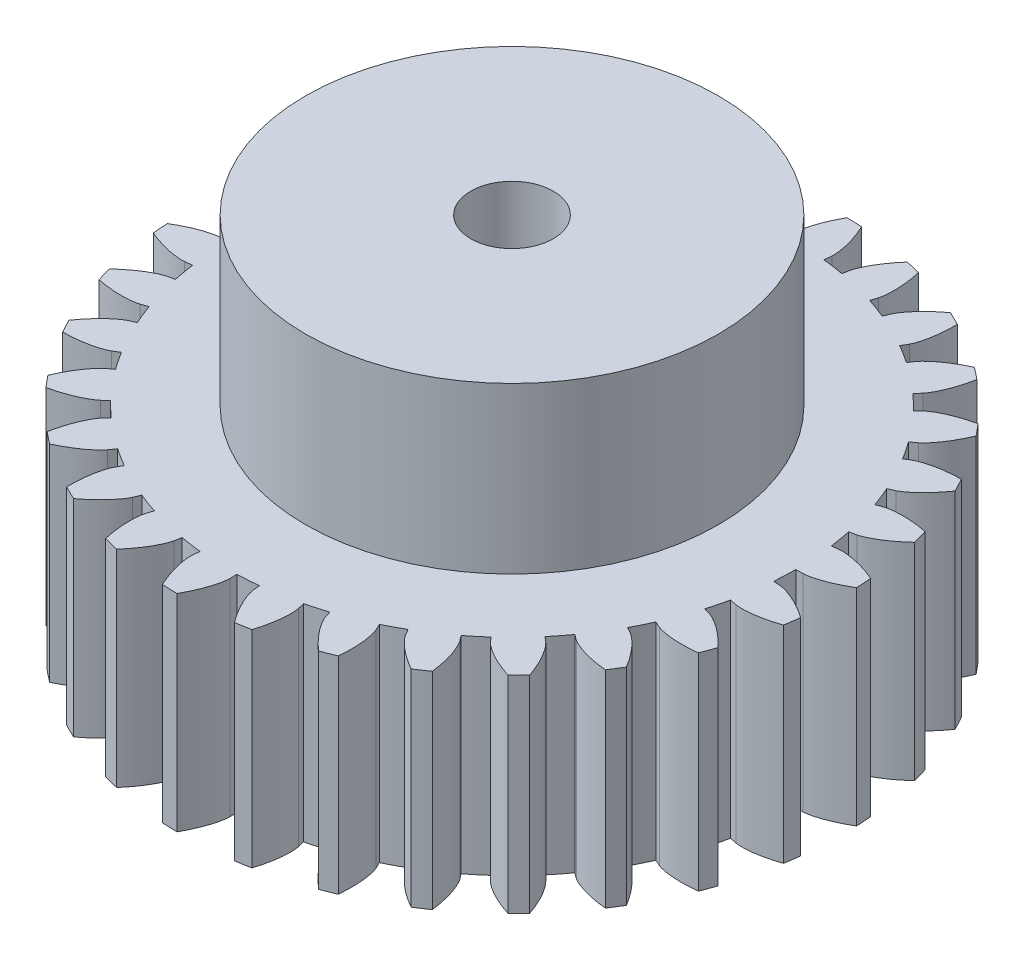
SolidWorks part; units mm, degrees
ref_plane "前视基准面" through (0, 0, 0) normal (0, 0, 1) x (1, 0, 0)
ref_plane "上视基准面" through (0, 0, 0) normal (0, 1, 0) x (1, 0, 0)
ref_plane "右视基准面" through (0, 0, 0) normal (1, 0, 0) x (0, 0, -1)
sketch "草图2" plane through (0, 0, 0) normal (0, 1, 0) x (1, 0, 0)
  line L0 (0, 0) -> (15.9638, 1.0755) construction
  line L1 (14.0954, 0) -> (13.75, 0)
  line L2 (13.968, 1.8907) -> (13.6257, 1.8444)
  circle A0 centre (0, 0) radius 14.0954
  circle A3 centre (0, 0) radius 13.75
  circle A4 centre (0, 0) radius 15
  circle A5 centre (0, 0) radius 16
  spline S0 degree 4 poles (14.0954, 0) (14.1222, 0.001) (14.1757, 0.0047) (14.282, 0.0185) (14.4824, 0.0575) (14.7468, 0.1297) (15.2365, 0.3049) (15.9787, 0.6703) (16.9045, 1.2915) (18.0602, 2.3363) (19.2165, 3.7493) (20.2505, 5.4679) (21.0984, 7.4555) (21.6937, 9.5315) (22.0508, 11.6608) (22.1898, 13.9217) (22.0692, 16.7242) (21.4978, 20.0254) (20.2807, 23.7245) (18.3101, 27.575) (15.8075, 31.1006) (13.2224, 33.8607) (10.7707, 35.9743) (8.5921, 37.5608) (6.7761, 38.7229) (4.4249, 40.0398) (1.9778, 41.1737) (-0.5458, 42.1227) (-3.6473, 43.04) (-6.016, 43.5621) (-8.1479, 43.8984) (-10.0201, 44.098) (-10.9657, 44.1742) (-11.7603, 44.2229) (-12.4935, 44.254) (-13.0612, 44.2726) (-13.8709, 44.2836) (-14.4735, 44.2825) (-15.466, 44.2663) (-16.2281, 44.2324) (-17.1613, 44.1817) (-17.9874, 44.1143) (-18.88, 44.0303) (-19.723, 43.9299) (-20.3853, 43.8424) (-20.8055, 43.7787) (-21.0244, 43.7455) knots 0 0 0 0 0 0.001401 0.002802 0.005604 0.010661 0.015718 0.02996 0.048734 0.068727 0.096889 0.125051 0.153212 0.181374 0.209535 0.237696 0.271429 0.327752 0.384075 0.440398 0.496721 0.553044 0.581206 0.609367 0.637529 0.66569 0.722013 0.750174 0.778336 0.834659 0.84874 0.86282 0.876901 0.883942 0.890982 0.900036 0.909091 0.920455 0.931818 0.943182 0.954545 0.965909 0.977273 0.988636 1 1 1 1 1 construction
  spline S1 degree 4 poles (14.0954, 0) (14.1222, 0.001) (14.1757, 0.0047) (14.282, 0.0185) (14.4824, 0.0575) (14.7468, 0.1297) (15.2365, 0.3049) (15.9787, 0.6703) (16.9045, 1.2915) (18.0602, 2.3363) (19.2165, 3.7493) (20.2505, 5.4679) (21.0984, 7.4555) (21.6937, 9.5315) (22.0508, 11.6608) (22.1898, 13.9217) (22.0692, 16.7242) (21.4978, 20.0254) (20.2807, 23.7245) (18.3101, 27.575) (15.8075, 31.1006) (13.2224, 33.8607) (10.7707, 35.9743) (8.5921, 37.5608) (6.7761, 38.7229) (4.4249, 40.0398) (1.9778, 41.1737) (-0.5458, 42.1227) (-3.6473, 43.04) (-6.016, 43.5621) (-8.1479, 43.8984) (-10.0201, 44.098) (-10.9657, 44.1742) (-11.7603, 44.2229) (-12.4935, 44.254) (-13.0612, 44.2726) (-13.6189, 44.2802) (-13.9379, 44.282) (-14.0954, 44.282) knots 0 0 0 0 0 0.001401 0.002802 0.005604 0.010661 0.015718 0.02996 0.048734 0.068727 0.096889 0.125051 0.153212 0.181374 0.209535 0.237696 0.271429 0.327752 0.384075 0.440398 0.496721 0.553044 0.581206 0.609367 0.637529 0.66569 0.722013 0.750174 0.778336 0.834659 0.84874 0.86282 0.876901 0.883942 0.890982 0.900036 0.909091 0.909091 0.909091 0.909091 0.909091
  spline S2 degree 4 poles (13.968, 1.8907) (13.9947, 1.8933) (14.0482, 1.8968) (14.1555, 1.8974) (14.3592, 1.8857) (14.631, 1.8495) (15.1397, 1.7416) (15.9242, 1.4791) (16.925, 0.9877) (18.2104, 0.1074) (19.5457, -1.1378) (20.801, -2.7021) (21.9077, -4.558) (22.7762, -6.5355) (23.4156, -8.5976) (23.8567, -10.8194) (24.1131, -13.6128) (23.9896, -16.9607) (23.2797, -20.7897) (21.8434, -24.8698) (19.8364, -28.6992) (17.6449, -31.7811) (15.4989, -34.2045) (13.5528, -36.0688) (11.909, -37.4641) (9.7557, -39.0844) (7.4828, -40.5363) (5.1093, -41.8153) (2.1589, -43.1402) (-0.1183, -43.9754) (-2.1859, -44.5946) (-4.0144, -45.0435) (-4.9412, -45.2459) (-5.7221, -45.4007) (-6.4445, -45.5299) (-7.0046, -45.6245) (-7.5562, -45.7068) (-7.8721, -45.7514) (-8.0281, -45.7725) knots 0 0 0 0 0 0.001401 0.002802 0.005604 0.010661 0.015718 0.02996 0.048734 0.068727 0.096889 0.125051 0.153212 0.181374 0.209535 0.237696 0.271429 0.327752 0.384075 0.440398 0.496721 0.553044 0.581206 0.609367 0.637529 0.66569 0.722013 0.750174 0.778336 0.834659 0.84874 0.86282 0.876901 0.883942 0.890982 0.900036 0.909091 0.909091 0.909091 0.909091 0.909091
  point P14 (14.9983, 0.2236)
  point P15 (15.9844, 0.7073)
  point P19 (14.9661, 1.0083)
  dimension "D1" = 27.5
  dimension "D2" = 28.1908
  dimension "D3" = 30
  dimension "D4" = 32
  dimension "D6" = 0.7854
extrude "凸台-拉伸1" add sketch "草图2" along normal blind 10
pattern_circular "阵列(圆周)1" count 30 over 360 about axis through (0, 10, 0) along (0, -1, 0) of "凸台-拉伸1"
sketch "草图3" plane through (0, 10, 0) normal (0, 1, 0) x (1, 0, 0)
  circle A0 centre (0, 0) radius 2
  dimension "D1" = 4
extrude "切除-拉伸1" cut sketch "草图3" against normal through all
sketch "草图4" plane through (0, 10, 0) normal (0, 1, 0) x (1, 0, 0)
  circle A0 centre (0, 0) radius 10
  circle A1 centre (0, 0) radius 2
  dimension "D1" = 20
extrude "凸台-拉伸2" add sketch "草图4" along normal blind 8
equation "\"m\"= 1'齿轮模数"
equation "\"z\"= 30'齿轮齿数"
equation "\"D\"= \"m\" * \"z\"'分度圆直径"
equation "\"Db\"= \"D\" * cos ( 20 )'基圆直径"
equation "\"Df\"= ( \"z\" - 2.5 ) * \"m\"'齿根圆直径"
equation "\"Da\"= ( \"z\" + 2 ) * \"m\"'齿顶圆直径"
equation "\"D1@草图2\"= \"Df\"'齿根圆"
equation "\"D2@草图2\"= \"Db\"'基圆"
equation "\"s\"= \"m\" * pi / 2'齿厚"
equation "\"D3@草图2\"= \"D\"'分度圆"
equation "\"D4@草图2\"= \"Da\"'齿顶圆"
equation "\"D6@草图2\"= \"s\" * 0.5"
